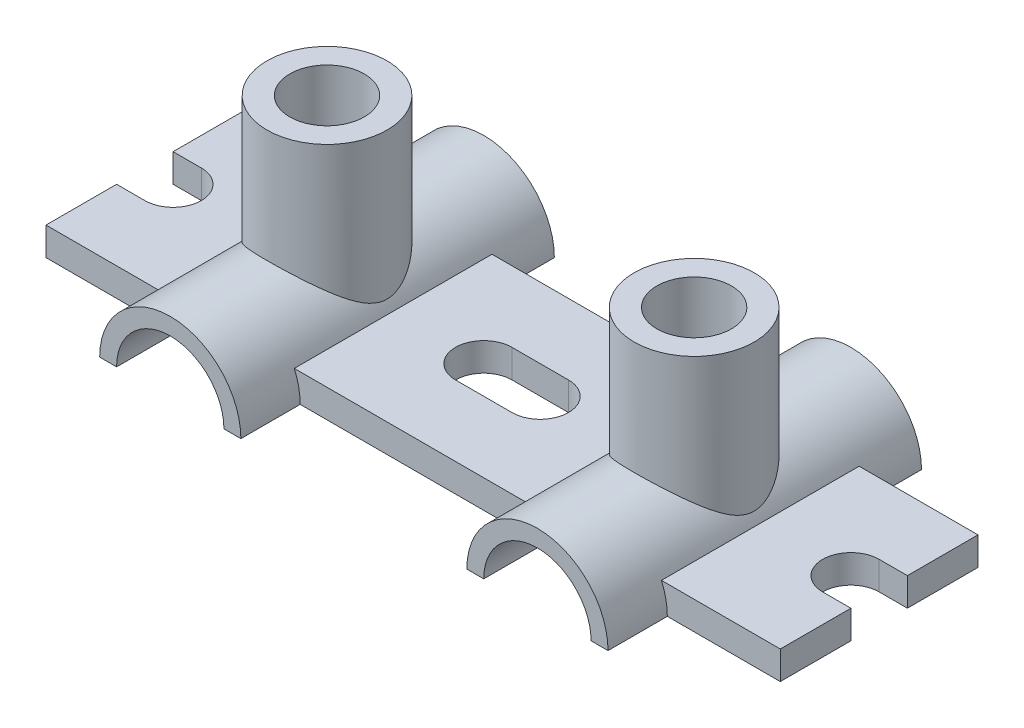
SolidWorks part; units mm, degrees
ref_plane "Front Plane" through (0, 0, 0) normal (0, 0, 1) x (1, 0, 0)
ref_plane "Top Plane" through (0, 0, 0) normal (0, 1, 0) x (1, 0, 0)
ref_plane "Right Plane" through (0, 0, 0) normal (1, 0, 0) x (0, 0, -1)
sketch "Sketch2" plane through (0, 0, 0) normal (0, 0, 1) x (1, 0, 0)
  line L0 (-19, 0) -> (0, 0) construction
  line L1 (-65, 0) -> (-19, 0)
  line L2 (-65, 0) -> (-65, 10)
  line L3 (-65, 10) -> (-22.9129, 10)
  line L4 (0, 50.3613) -> (0, -44.652) construction
  line L5 (65, 0) -> (65, 10)
  line L6 (65, 10) -> (22.9129, 10)
  line L7 (65, 0) -> (19, 0)
  arc A2 (19, 0) -> (-19, 0) centre (0, 0) ccw
  arc A3 (22.9129, 10) -> (-22.9129, 10) centre (0, 0) ccw
  dimension "D1" = 38
  dimension "D2" = 50
  dimension "D4" = 10
extrude "Boss-Extrude1" add sketch "Sketch2" along normal blind 110
sketch "Sketch3" plane through (0, 10, 0) normal (0, 1, 0) x (1, 0, 0)
  line L0 (65, -55) -> (143.1694, -55) construction
  line L1 (65, -45) -> (55, -45)
  line L2 (65, -110) -> (65, 0) construction
  line L3 (55, -45) -> (55, -69.9886) construction
  line L4 (65, -55) -> (0, -55) construction
  line L5 (22.9129, 0) -> (22.9129, -20)
  line L6 (22.9129, -110) -> (22.9129, 0) construction
  line L7 (22.9129, -20) -> (65, -20)
  line L8 (65, -55) -> (65, -45)
  line L9 (65, -65) -> (55, -65)
  line L10 (22.9129, -110) -> (22.9129, -90)
  line L11 (22.9129, -90) -> (65, -90)
  line L12 (22.9129, -110) -> (65, -110)
  line L13 (65, -20) -> (65, 0)
  line L14 (65, 0) -> (22.9129, 0)
  line L15 (65, -90) -> (65, -110)
  line L16 (65, -45) -> (65, -65)
  line L17 (0, 0) -> (0, -128.8272) construction
  line L18 (-65, -90) -> (-65, -110)
  line L19 (-22.9129, -110) -> (-65, -110)
  line L20 (-22.9129, -110) -> (-22.9129, -90)
  line L21 (-22.9129, -90) -> (-65, -90)
  line L22 (-65, -45) -> (-65, -65)
  line L23 (-65, -65) -> (-55, -65)
  line L24 (-65, -45) -> (-55, -45)
  line L25 (-22.9129, -20) -> (-65, -20)
  line L26 (-22.9129, 0) -> (-22.9129, -20)
  line L27 (-65, 0) -> (-22.9129, 0)
  line L28 (-65, -20) -> (-65, 0)
  arc A0 (55, -45) -> (55, -65) centre (55, -55) ccw
  arc A1 (-55, -45) -> (-55, -65) centre (-55, -55) cw
  line M2 (65, 0) -> (22.9129, 0)
  line M3 (22.9129, 0) -> (22.9129, -110)
  line M4 (22.9129, -110) -> (65, -110)
  line M5 (65, -110) -> (65, 0)
  dimension "D1" = 20
sketch "Sketch4" plane through (0, 10, 0) normal (0, 1, 0) x (1, 0, 0)
extrude "Cut-Extrude3" cut sketch "Sketch3" against normal through all both and the other way through all contours L7 M3 M5 M2 | L1 A0 L9 M5 | L11 M3 M4 M5
ref_plane "Plane1" through (0, 0, 0) normal (1, 0, 0) x (0, 0, -1)
mirror "Mirror1" about plane through (0, 0, 0) normal (1, 0, 0) of "Cut-Extrude3"
sketch "Sketch7" plane through (0, 0, 20) normal (0, 0, -1) x (-1, 0, 0)
  line L0 (-71.5777, 0) -> (-19, 0) construction
  line L1 (19, 0) -> (84.4196, 0) construction
  line L2 (-25, 0) -> (-19, 0)
  line L3 (19, 0) -> (25, 0)
  arc A0 (25, 0) -> (-25, 0) centre (0, 0) ccw
  arc A1 (19, 0) -> (-19, 0) centre (0, 0) ccw
  dimension "D1" = 50
  dimension "D2" = 38
extrude "Boss-Extrude4" add sketch "Sketch7" along normal blind 20 and the other way blind 91
ref_plane "Plane2" through (0, 65, 0) normal (0, 1, 0) x (1, 0, 0)
sketch "Sketch8" plane through (0, 65, 0) normal (0, 1, 0) x (1, 0, 0)
  line L0 (-25, 0) -> (25, -111) construction
  line L1 (-25, -111) -> (25, 0) construction
  line L2 (25, -20) -> (25, 0) construction
  circle A0 centre (0, -55.5) radius 21.2583
  circle A1 centre (0, -55.5) radius 13.1986
extrude "Boss-Extrude5" add sketch "Sketch8" against normal up to surface (40 mm away)
sketch "Sketch9" plane through (0, 65, 0) normal (0, 1, 0) x (1, 0, 0)
  circle A0 centre (0, -55.5) radius 13.1986
extrude "Cut-Extrude4" cut sketch "Sketch9" against normal blind 49
ref_plane "Plane3" through (65, 0, 0) normal (1, 0, 0) x (0, 0, -1)
mirror "Mirror2" about plane through (65, 0, 0) normal (1, 0, 0) of bodies 111
